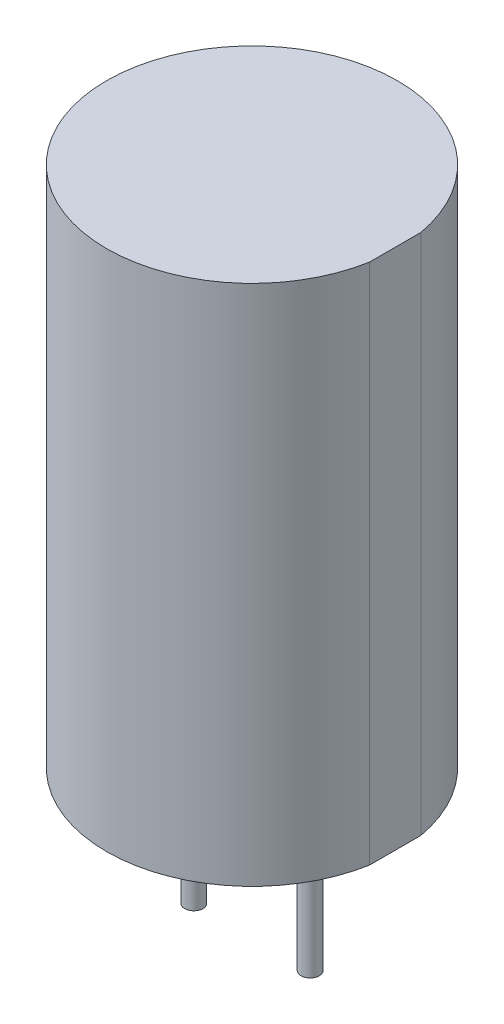
SolidWorks part; units mm, degrees
ref_plane "Front Plane" through (0, 0, 0) normal (0, 0, 1) x (1, 0, 0)
ref_plane "Top Plane" through (0, 0, 0) normal (0, 1, 0) x (1, 0, 0)
ref_plane "Right Plane" through (0, 0, 0) normal (1, 0, 0) x (0, 0, -1)
sketch "Sketch1" plane through (0, 0, 0) normal (0, 1, 0) x (1, 0, 0)
  line L0 (3.125, 0.5612) -> (3.125, -0.5612)
  arc A0 (3.125, 0.5612) -> (3.125, -0.5612) centre (0, 0) ccw
  dimension "D1" = 6.35
  dimension "D2" = 3.125
extrude "Boss-Extrude1" add sketch "Sketch1" along normal blind 11.4
sketch "Sketch2" plane through (0, 0, 0) normal (0, -1, 0) x (1, 0, 0)
  circle A0 centre (-1.27, 0) radius 0.2
  circle A1 centre (1.27, 0) radius 0.2
  dimension "D1" = 0.4
  dimension "D2" = 2.54
  dimension "D3" = 1.27
extrude "Boss-Extrude2" add sketch "Sketch2" along normal blind 3.2
equation "\"D2@Sketch1\"=\"D1@Sketch1\"/2-0.05"
equation "\"D3@Sketch2\"=\"D2@Sketch2\"/2"
